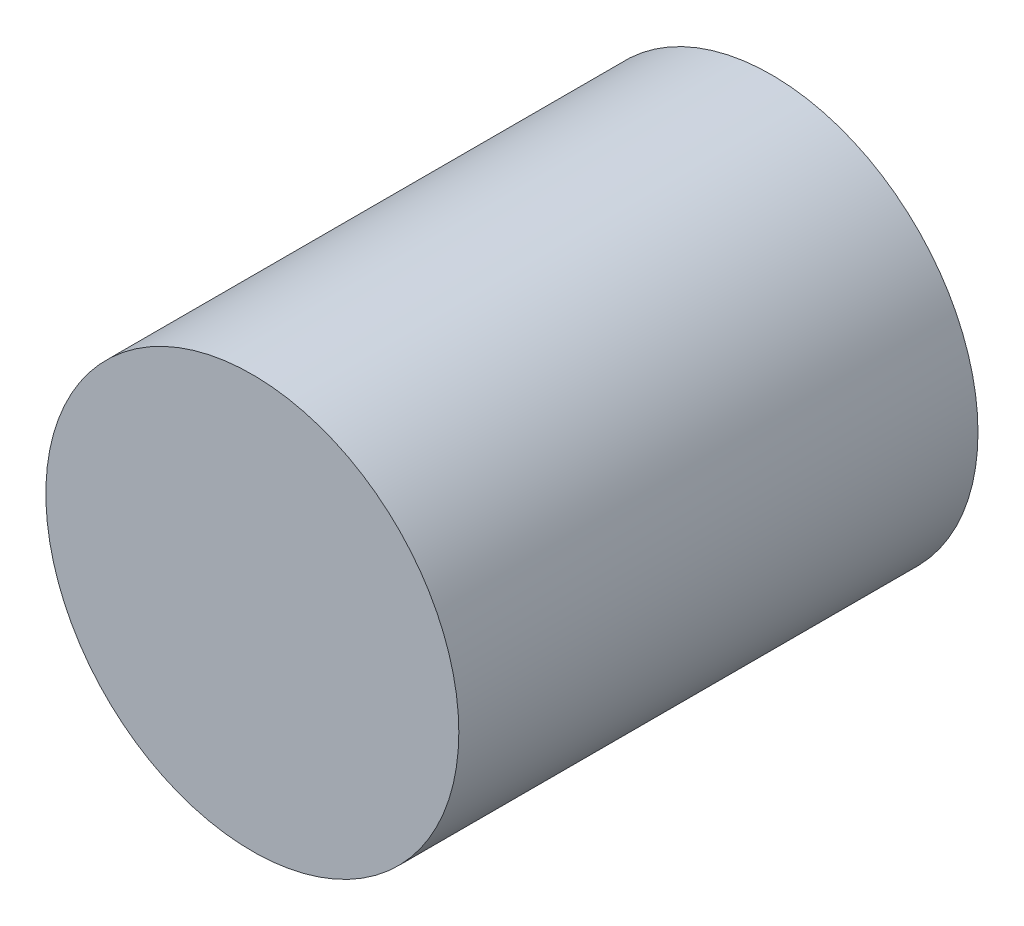
SolidWorks part; units mm, degrees
material "Plain Carbon Steel"
ref_plane "Front Plane" through (0, 0, 0) normal (0, 0, 1) x (1, 0, 0)
ref_plane "Top Plane" through (0, 0, 0) normal (0, 1, 0) x (1, 0, 0)
ref_plane "Right Plane" through (0, 0, 0) normal (1, 0, 0) x (0, 0, -1)
sketch "Sketch1" plane through (0, 0, 0) normal (0, 0, 1) x (1, 0, 0)
  circle A0 centre (0, 0) radius 17.5
  dimension "D1" = 35
extrude "Boss-Extrude1" add sketch "Sketch1" along normal blind 44
